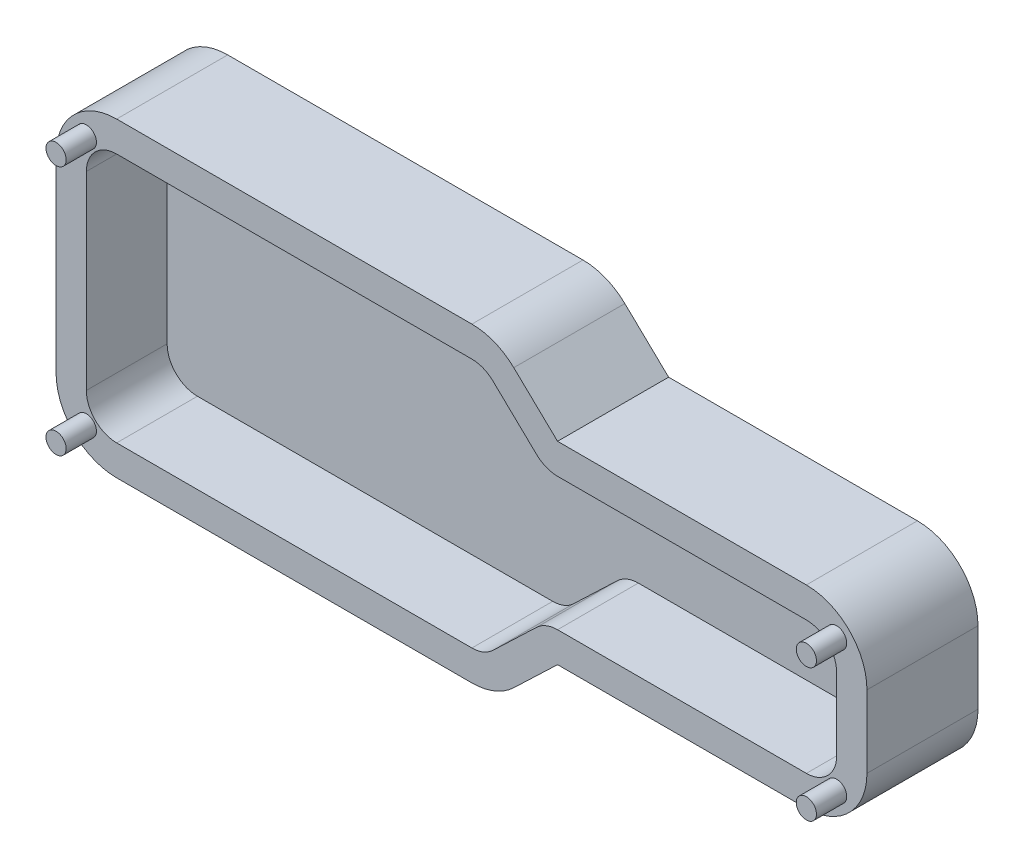
SolidWorks part; units mm, degrees
ref_plane "Front Plane" through (0, 0, 0) normal (0, 0, 1) x (1, 0, 0)
ref_plane "Top Plane" through (0, 0, 0) normal (0, 1, 0) x (1, 0, 0)
ref_plane "Right Plane" through (0, 0, 0) normal (1, 0, 0) x (0, 0, -1)
sketch "Sketch2" plane through (0, 0, 0) normal (0, 0, 1) x (1, 0, 0)
  line L0 (-34.29, 10.16) -> (0, 10.16)
  line L1 (-34.29, 10.16) -> (-34.29, 0)
  line L2 (-34.29, 0) -> (0, 0)
  line L3 (0, 10.16) -> (0, 0)
  line L4 (-69.31, 13.97) -> (-36.29, 13.97)
  line L5 (-69.31, 13.97) -> (-69.31, -3.81)
  line L6 (-69.31, -3.81) -> (-36.29, -3.81)
  line L7 (-36.29, 13.97) -> (-36.29, -3.81)
  line L8 (-31.29, 10.16) -> (-31.29, 0)
  line L9 (-71.31, 15.97) -> (-34.29, 15.97)
  line L10 (-34.29, 15.97) -> (-34.29, 12.16)
  line L11 (-34.29, 12.16) -> (-31.29, 12.16)
  line L12 (-31.29, 12.16) -> (-31.29, -2)
  line L13 (-31.29, -2) -> (-34.29, -2)
  line L14 (-34.29, -2) -> (-34.29, -5.81)
  line L15 (-34.29, -5.81) -> (-71.31, -5.81)
  line L16 (-71.31, -5.81) -> (-71.31, 15.97)
  point P4 (-34.29, 5.08)
  point P5 (-36.29, 5.08)
  dimension "D1" = 2
  dimension "D2" = 2
  dimension "D3" = 2
  dimension "D5" = 2
  dimension "D4" = 2
  dimension "D6" = 0
sketch "Sketch3" plane through (0, 0, 0) normal (0, 0, 1) x (1, 0, 0)
  line L0 (-69.81, 17.47) -> (-34.6251, 17.47)
  line L1 (-32.5518, 16.6383) -> (-28.2152, 12.4917)
  line L2 (-26.1419, 11.66) -> (-1.5, 11.66)
  line L3 (1.5, 8.66) -> (1.5, 1.5)
  line L4 (-1.5, -1.5) -> (-26.1419, -1.5)
  line L5 (-28.2152, -2.3317) -> (-32.5518, -6.4783)
  line L6 (-34.6251, -7.31) -> (-69.81, -7.31)
  line L7 (-72.81, -4.31) -> (-72.81, 14.47)
  line L8 (-71.31, 15.97) -> (-34.29, 15.97) construction
  line L9 (-34.29, -5.81) -> (-71.31, -5.81) construction
  line L11 (-34.29, 0) -> (0, 0) construction
  line L12 (0, 10.16) -> (0, 0) construction
  line L13 (-71.31, -5.81) -> (-71.31, 15.97) construction
  line L14 (-69.81, 20.47) -> (-34.6251, 20.47)
  line L15 (-30.4785, 18.8066) -> (-26.1419, 14.66)
  line L16 (-26.1419, 14.66) -> (-1.5, 14.66)
  line L17 (4.5, 8.66) -> (4.5, 1.5)
  line L18 (-1.5, -4.5) -> (-26.1419, -4.5)
  line L19 (-26.1419, -4.5) -> (-30.4785, -8.6466)
  line L20 (-34.6251, -10.31) -> (-69.81, -10.31)
  line L21 (-75.81, -4.31) -> (-75.81, 14.47)
  arc A0 (-69.81, -7.31) -> (-72.81, -4.31) centre (-69.81, -4.31) cw
  arc A1 (-1.5, 11.66) -> (1.5, 8.66) centre (-1.5, 8.66) cw
  arc A2 (1.5, 1.5) -> (-1.5, -1.5) centre (-1.5, 1.5) cw
  arc A3 (-32.5518, -6.4783) -> (-34.6251, -7.31) centre (-34.6251, -4.31) cw
  arc A4 (-26.1419, -1.5) -> (-28.2152, -2.3317) centre (-26.1419, -4.5) ccw
  arc A5 (-28.2152, 12.4917) -> (-26.1419, 11.66) centre (-26.1419, 14.66) ccw
  arc A6 (-34.6251, 17.47) -> (-32.5518, 16.6383) centre (-34.6251, 14.47) cw
  arc A7 (-69.81, 17.47) -> (-72.81, 14.47) centre (-69.81, 14.47) ccw
  arc A8 (-34.6251, 20.47) -> (-30.4785, 18.8066) centre (-34.6251, 14.47) cw
  arc A9 (-26.1419, 14.66) -> (-26.1419, 14.66) centre (-26.1419, 14.66) ccw
  arc A10 (-1.5, 14.66) -> (4.5, 8.66) centre (-1.5, 8.66) cw
  arc A11 (4.5, 1.5) -> (-1.5, -4.5) centre (-1.5, 1.5) cw
  arc A12 (-26.1419, -4.5) -> (-26.1419, -4.5) centre (-26.1419, -4.5) ccw
  arc A13 (-30.4785, -8.6466) -> (-34.6251, -10.31) centre (-34.6251, -4.31) cw
  arc A14 (-69.81, -10.31) -> (-75.81, -4.31) centre (-69.81, -4.31) cw
  arc A15 (-69.81, 20.47) -> (-75.81, 14.47) centre (-69.81, 14.47) ccw
  circle A16 centre (-72.81, 17.47) radius 1
  circle A17 centre (-72.81, -7.31) radius 1
  circle A18 centre (1.5, -1.5) radius 1
  circle A19 centre (1.5, 11.66) radius 1
  point P26 (-33.4216, -7.31)
  point P29 (-27.3454, -1.5)
  point P32 (-27.3454, 11.66)
  point P35 (-33.4216, 17.47)
  dimension "D5" = 3
  dimension "D6" = 2
  dimension "D1" = 1.5
  dimension "D2" = 1.5
  dimension "D3" = 1.5
  dimension "D4" = 1.5
extrude "Boss-Extrude2" add sketch "Sketch3" along normal blind 8 and the other way blind 3
sketch "Sketch5" plane through (0, 0, -3) normal (0, 0, -1) x (-1, 0, 0)
  line L0 (-1.5, 1.5) -> (-1.5, 8.66) construction
  line L1 (26.1419, -1.5) -> (1.5, -1.5) construction
  line L2 (32.5518, -6.4783) -> (28.2152, -2.3317) construction
  line L3 (69.81, -7.31) -> (34.6251, -7.31) construction
  line L4 (72.81, 14.47) -> (72.81, -4.31) construction
  line L5 (-1.5, 1.5) -> (-1.5, 8.66)
  line L6 (26.1419, -1.5) -> (1.5, -1.5)
  line L7 (32.5518, -6.4783) -> (28.2152, -2.3317)
  line L8 (72.81, -4.31) -> (72.81, 14.47)
  line L9 (34.6251, -7.31) -> (69.81, -7.31)
  line L10 (28.2152, -2.3317) -> (32.5518, -6.4783)
  line L11 (1.5, -1.5) -> (26.1419, -1.5)
  line L12 (-1.5, 8.66) -> (-1.5, 1.5)
  line L13 (26.1419, 11.66) -> (1.5, 11.66)
  line L14 (32.5518, 16.6383) -> (28.2152, 12.4917)
  line L15 (69.81, 17.47) -> (34.6251, 17.47)
  line L16 (72.81, -4.31) -> (72.81, 14.47)
  line L17 (34.6251, -7.31) -> (69.81, -7.31)
  line L18 (28.2152, -2.3317) -> (32.5518, -6.4783)
  line L19 (1.5, -1.5) -> (26.1419, -1.5)
  line L20 (-1.5, 8.66) -> (-1.5, 1.5)
  line L21 (26.1419, 11.66) -> (1.5, 11.66)
  line L22 (32.5518, 16.6383) -> (28.2152, 12.4917)
  line L23 (69.81, 17.47) -> (34.6251, 17.47)
  line L24 (69.81, -7.31) -> (34.6251, -7.31)
  line L25 (72.81, 14.47) -> (72.81, -4.31)
  arc A0 (1.5, 11.66) -> (-1.5, 8.66) centre (1.5, 8.66) ccw construction
  arc A1 (-1.5, 1.5) -> (1.5, -1.5) centre (1.5, 1.5) ccw construction
  arc A2 (28.2152, -2.3317) -> (26.1419, -1.5) centre (26.1419, -4.5) ccw construction
  arc A3 (32.5518, -6.4783) -> (34.6251, -7.31) centre (34.6251, -4.31) ccw construction
  arc A4 (69.81, -7.31) -> (72.81, -4.31) centre (69.81, -4.31) ccw construction
  arc A5 (72.81, 14.47) -> (69.81, 17.47) centre (69.81, 14.47) ccw construction
  arc A6 (1.5, 11.66) -> (-1.5, 8.66) centre (1.5, 8.66) ccw
  arc A7 (-1.5, 1.5) -> (1.5, -1.5) centre (1.5, 1.5) ccw
  arc A8 (69.81, -7.31) -> (72.81, -4.31) centre (69.81, -4.31) ccw
  arc A9 (32.5518, -6.4783) -> (34.6251, -7.31) centre (34.6251, -4.31) ccw
  arc A10 (28.2152, -2.3317) -> (26.1419, -1.5) centre (26.1419, -4.5) ccw
  arc A11 (-1.5, 1.5) -> (1.5, -1.5) centre (1.5, 1.5) ccw
  arc A12 (1.5, 11.66) -> (-1.5, 8.66) centre (1.5, 8.66) ccw
  arc A13 (26.1419, 11.66) -> (28.2152, 12.4917) centre (26.1419, 14.66) ccw
  arc A14 (34.6251, 17.47) -> (32.5518, 16.6383) centre (34.6251, 14.47) ccw
  arc A15 (72.81, 14.47) -> (69.81, 17.47) centre (69.81, 14.47) ccw
  arc A16 (69.81, -7.31) -> (72.81, -4.31) centre (69.81, -4.31) ccw
  arc A17 (32.5518, -6.4783) -> (34.6251, -7.31) centre (34.6251, -4.31) ccw
  arc A18 (28.2152, -2.3317) -> (26.1419, -1.5) centre (26.1419, -4.5) ccw
  arc A19 (-1.5, 1.5) -> (1.5, -1.5) centre (1.5, 1.5) ccw
  arc A20 (1.5, 11.66) -> (-1.5, 8.66) centre (1.5, 8.66) ccw
  arc A21 (26.1419, 11.66) -> (28.2152, 12.4917) centre (26.1419, 14.66) ccw
  arc A22 (34.6251, 17.47) -> (32.5518, 16.6383) centre (34.6251, 14.47) ccw
  arc A23 (72.81, 14.47) -> (69.81, 17.47) centre (69.81, 14.47) ccw
  arc A24 (28.2152, -2.3317) -> (26.1419, -1.5) centre (26.1419, -4.5) ccw
  arc A25 (32.5518, -6.4783) -> (34.6251, -7.31) centre (34.6251, -4.31) ccw
  arc A26 (69.81, -7.31) -> (72.81, -4.31) centre (69.81, -4.31) ccw
  arc A27 (72.81, 14.47) -> (69.81, 17.47) centre (69.81, 14.47) ccw
  line M17 (72.81, 14.47) -> (72.81, -4.31)
  arc M18 (72.81, -4.31) -> (69.81, -7.31) centre (69.81, -4.31) cw
  line M19 (69.81, -7.31) -> (34.6251, -7.31)
  arc M20 (34.6251, -7.31) -> (32.5518, -6.4783) centre (34.6251, -4.31) cw
  line M21 (32.5518, -6.4783) -> (28.2152, -2.3317)
  arc M22 (28.2152, -2.3317) -> (26.1419, -1.5) centre (26.1419, -4.5) ccw
  line M23 (26.1419, -1.5) -> (1.5, -1.5)
  arc M24 (1.5, -1.5) -> (-1.5, 1.5) centre (1.5, 1.5) cw
  line M25 (-1.5, 1.5) -> (-1.5, 8.66)
  arc M26 (-1.5, 8.66) -> (1.5, 11.66) centre (1.5, 8.66) cw
  line M27 (1.5, 11.66) -> (26.1419, 11.66)
  arc M28 (26.1419, 11.66) -> (28.2152, 12.4917) centre (26.1419, 14.66) ccw
  line M29 (28.2152, 12.4917) -> (32.5518, 16.6383)
  arc M30 (32.5518, 16.6383) -> (34.6251, 17.47) centre (34.6251, 14.47) cw
  line M31 (34.6251, 17.47) -> (69.81, 17.47)
  arc M32 (69.81, 17.47) -> (72.81, 14.47) centre (69.81, 14.47) cw
  dimension "D1" = 0
extrude "Boss-Extrude3" add sketch "Sketch5" against normal blind 3 contours M17 M32 M31 M30 M29 M28 M27 M26 M25 M24 M23 M22 M21 M20 M19 M18
sketch "Sketch7" plane through (0, 0, 8) normal (0, 0, 1) x (1, 0, 0)
  circle A0 centre (-72.81, 17.47) radius 1 construction
  circle A1 centre (-72.81, 17.47) radius 1
  circle A2 centre (1.5, -1.5) radius 1 construction
  circle A3 centre (1.5, -1.5) radius 1
  circle A4 centre (1.5, 11.66) radius 1 construction
  circle A5 centre (1.5, 11.66) radius 1
  circle A6 centre (-72.81, -7.31) radius 1 construction
  circle A7 centre (-72.81, -7.31) radius 1
extrude "Boss-Extrude4" add sketch "Sketch7" against normal blind 11 and the other way blind 3
equation "\"D5@Sketch2\"=\"pcb_overflow\""
equation "\"D1@Sketch2\"=\"pcb_overflow\""
equation "\"D2@Sketch2\"=\"pcb_overflow\""
equation "\"D4@Sketch2\"=\"pcb_overflow\""
equation "\"D3@Sketch2\"=\"pcb_overflow\""
equation "\"D1@Sketch3\"=\"gap_from_case\""
equation "\"D2@Sketch3\"=\"gap_from_case\""
equation "\"D3@Sketch3\"=\"gap_from_case\""
equation "\"D4@Sketch3\"=\"gap_from_case\""
equation "\"D6@Sketch3\"=\"notch_dia\""
